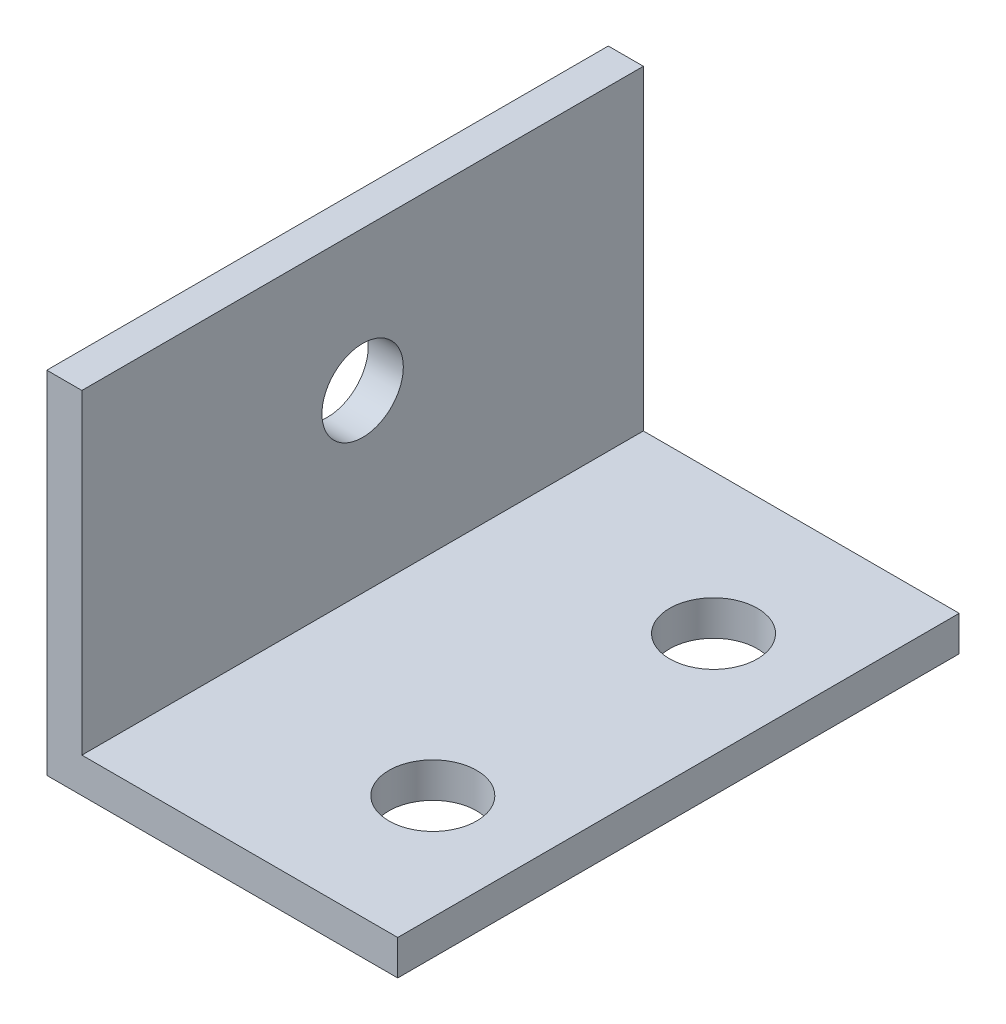
SolidWorks part; units mm, degrees
ref_plane "Front Plane" through (0, 0, 0) normal (0, 0, 1) x (1, 0, 0)
ref_plane "Top Plane" through (0, 0, 0) normal (0, 1, 0) x (1, 0, 0)
ref_plane "Right Plane" through (0, 0, 0) normal (1, 0, 0) x (0, 0, -1)
sketch "Sketch1" plane through (0, 0, 0) normal (0, 0, 1) x (1, 0, 0)
  line L0 (3.175, 3.175) -> (0, 3.175) construction
  line L1 (0, 0) -> (3.175, 0)
  line L2 (0, 0) -> (0, 31.75)
  line L3 (0, 31.75) -> (3.175, 31.75)
  line L4 (3.175, 0) -> (3.175, 31.75)
  line L5 (3.175, 0) -> (31.75, 0)
  line L6 (3.175, 0) -> (3.175, 3.175)
  line L7 (3.175, 3.175) -> (31.75, 3.175)
  line L8 (31.75, 0) -> (31.75, 3.175)
  line L9 (1.5875, 3.175) -> (1.5875, 31.75) construction
  point P11 (1.5875, 17.4625)
  dimension "D1" = 3.175
  dimension "D2" = 3.175
  dimension "D3" = 31.75
  dimension "D4" = 31.75
extrude "Boss-Extrude1" add sketch "Sketch1" along normal blind 50.8 contours L1 L4 L3 L2 | L5 L8 L7 L4
sketch "Sketch2" plane through (3.175, 0, 0) normal (1, 0, 0) x (0, 0, -1)
  line L0 (-50.8, 3.175) -> (-50.8, 31.75) construction
  line L1 (-50.8, 31.75) -> (0, 31.75) construction
  line L2 (0, 31.75) -> (0, 3.175) construction
  line L3 (0, 3.175) -> (-50.8, 3.175) construction
  line L4 (-50.8, 19.05) -> (0, 19.05) construction
  line L5 (-25.4, 31.75) -> (-25.4, 3.175) construction
  circle A0 centre (-25.4, 19.05) radius 3.683
  circle A1 centre (-25.4, 19.05) radius 10.4013 construction
  circle A2 centre (-25.4, 19.05) radius 8.8138 construction
  dimension "D1" = 7.366
  dimension "D2" = 20.8026
  dimension "D3" = 17.6276
  dimension "D4" = 15.875
extrude "Pot Mount" cut sketch "Sketch2" against normal up to next
sketch "Sketch3" plane through (0, 3.175, 0) normal (0, 1, 0) x (1, 0, 0)
  line L0 (3.175, -50.8) -> (31.75, -50.8) construction
  line L1 (31.75, -50.8) -> (31.75, 0) construction
  line L2 (31.75, 0) -> (3.175, 0) construction
  line L3 (3.175, 0) -> (3.175, -50.8) construction
  line L4 (22.225, -50.8) -> (22.225, 0) construction
  circle A0 centre (22.225, -38.1) radius 3.9688
  circle A1 centre (22.225, -12.7) radius 3.9688
  dimension "D2" = 7.9375
  dimension "D3" = 7.9375
  dimension "D1" = 9.525
  dimension "D4" = 25.4
  dimension "D5" = 12.7
extrude "Base Mount" cut sketch "Sketch3" against normal up to next
